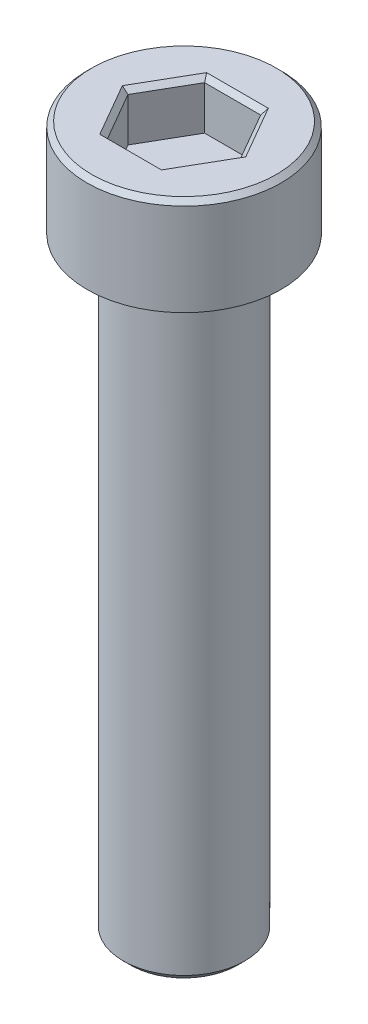
SolidWorks part; units mm, degrees
ref_plane "前视基准面" through (0, 0, 0) normal (0, 0, 1) x (1, 0, 0)
ref_plane "上视基准面" through (0, 0, 0) normal (0, 1, 0) x (1, 0, 0)
ref_plane "右视基准面" through (0, 0, 0) normal (1, 0, 0) x (0, 0, -1)
sketch "草图1" plane through (0, 0, 0) normal (0, 1, 0) x (1, 0, 0)
  circle A0 centre (0, 0) radius 4
  dimension "D1" = 8
extrude "凸台-拉伸1" add sketch "草图1" along normal blind 4
sketch "草图2" plane through (0, 0, 0) normal (0, -1, 0) x (1, 0, 0)
  circle A0 centre (0, 0) radius 2.5
  dimension "D1" = 5
extrude "凸台-拉伸2" add sketch "草图2" along normal blind 25
cosmetic thread "装饰螺纹线1" parameters "D2"=4
sketch "草图11" plane through (0, 4, 0) normal (0, 1, 0) x (1, 0, 0)
  line L1 (1.155, 1.9999) -> (-1.1544, 2.0001)
  line L2 (-1.1544, 2.0001) -> (-2.3094, 0.0003)
  line L3 (-2.3094, 0.0003) -> (-1.155, -1.9999)
  line L4 (-1.155, -1.9999) -> (1.1544, -2.0001)
  line L5 (1.1544, -2.0001) -> (2.3094, -0.0003)
  line L6 (2.3094, -0.0003) -> (1.155, 1.9999)
  circle A0 centre (0, 0) radius 2 construction
  dimension "D1" = 4
extrude "切除-拉伸1" cut sketch "草图11" against normal blind 2
chamfer "倒角1" distance 0.2 angle 45 7 edges at (0, 4, 4) (0.0003, 4, -2) (-1.7319, 4, -1.0002) (-1.7322, 4, 0.9998) (-0.0003, 4, 2) (1.7319, 4, 1.0002) (1.7322, 4, -0.9998)
chamfer "倒角2" distance 0.3 angle 45 1 edges at (0, -25, -2.5)
